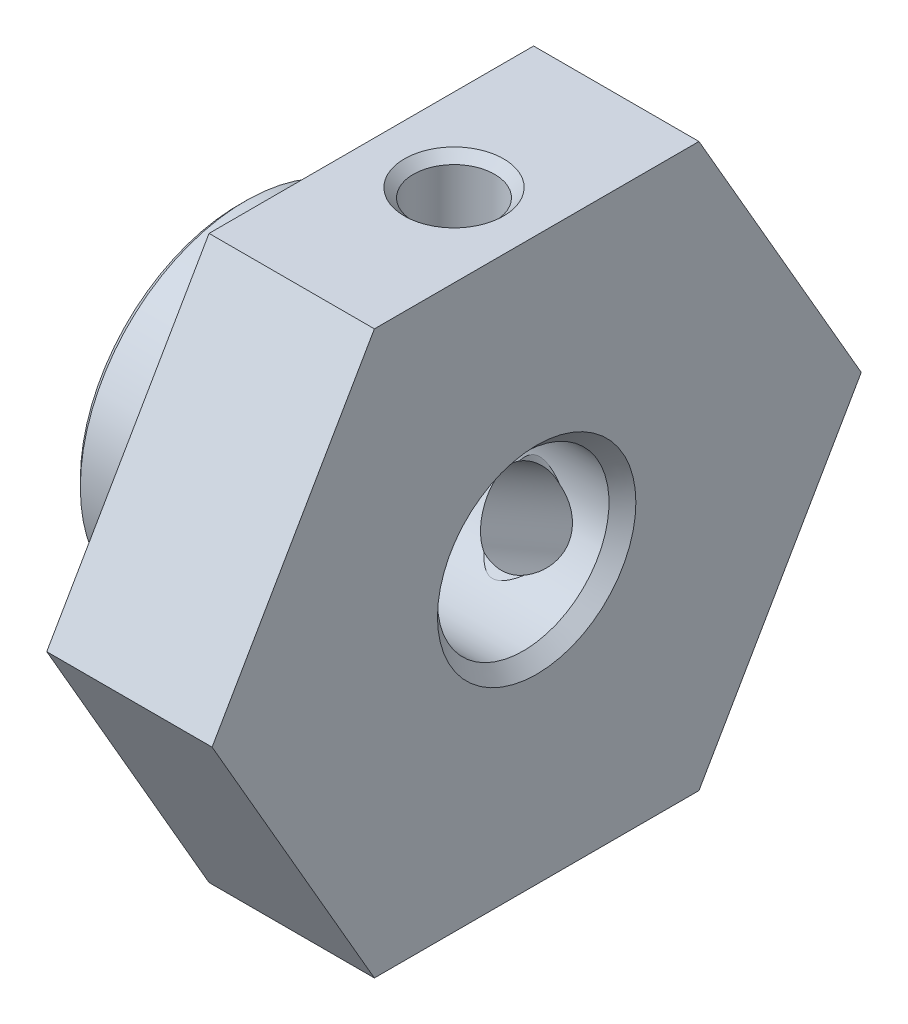
SolidWorks part; units mm, degrees
ref_plane "Front Plane" through (0, 0, 0) normal (0, 0, 1) x (1, 0, 0)
ref_plane "Top Plane" through (0, 0, 0) normal (0, 1, 0) x (1, 0, 0)
ref_plane "Right Plane" through (0, 0, 0) normal (1, 0, 0) x (0, 0, -1)
ref_plane "Plane1" through (0, 0, 0) normal (0, 0, 1) x (1, 0, 0)
sketch "Sketch1" plane through (0, 0, 0) normal (0, 0, 1) x (1, 0, 0)
  line L0 (0, 0) -> (0, 4.8)
  line L1 (0, 4.8) -> (0.2, 5)
  line L2 (0.2, 5) -> (4, 5)
  line L3 (4, 5) -> (4, 10.2)
  line L4 (4, 10.2) -> (9, 10.2)
  line L5 (9, 10.2) -> (9, 0)
  line L6 (9, 0) -> (0, 0)
  line L7 (9, 0) -> (0, 0) construction
revolve "Revolve1" add sketch "Sketch1" angle 360 about L7
ref_plane "Plane2" through (0, 0, 0) normal (0, 0, 1) x (1, 0, 0)
sketch "Sketch2" plane through (0, 0, 0) normal (0, 0, 1) x (1, 0, 0)
  line L0 (0, 0) -> (0, 3)
  line L1 (0, 3) -> (0.406, 2.594)
  line L2 (0.406, 2.594) -> (8.594, 2.594)
  line L3 (8.594, 2.594) -> (9, 3)
  line L4 (9, 3) -> (9, 0)
  line L5 (9, 0) -> (0, 0)
  line L6 (9, 0) -> (0, 0) construction
revolve "Cut-Revolve1" cut sketch "Sketch2" angle 360 about L6
ref_plane "Plane3" through (0, 0, 0) normal (1, 0, 0) x (0, 0, -1)
sketch "Sketch3" plane through (0, 0, 0) normal (1, 0, 0) x (0, 0, -1)
  line L0 (-17, -17) -> (17, -17)
  line L1 (17, -17) -> (17, 17)
  line L2 (17, 17) -> (-17, 17)
  line L3 (-17, 17) -> (-17, -17)
  line L4 (-9.815, 0) -> (-4.9075, -8.5)
  line L5 (-4.9075, -8.5) -> (4.9075, -8.5)
  line L6 (4.9075, -8.5) -> (9.815, 0)
  line L7 (9.815, 0) -> (4.9075, 8.5)
  line L8 (4.9075, 8.5) -> (-4.9075, 8.5)
  line L9 (-4.9075, 8.5) -> (-9.815, 0)
extrude "Cut-Extrude1" cut sketch "Sketch3" along normal blind 9
ref_plane "Plane4" through (6.5, 0, 0) normal (1, 0, 0) x (0, 0, -1)
sketch "Sketch4" plane through (6.5, 0, 0) normal (1, 0, 0) x (0, 0, -1)
  line L0 (0, 8.5) -> (1.5, 8.5)
  line L1 (1.5, 8.5) -> (1.2295, 8.2295)
  line L2 (1.2295, 8.2295) -> (1.2295, 2.3645)
  line L3 (1.2295, 2.3645) -> (1.5, 2.094)
  line L4 (1.5, 2.094) -> (0, 2.094)
  line L5 (0, 2.094) -> (0, 8.5)
  line L6 (0, 2.094) -> (0, 8.5) construction
revolve "Cut-Revolve2" cut sketch "Sketch4" angle 360 about L6
ref_plane "Plane5" through (6.5, 0, 0) normal (1, 0, 0) x (0, 0, -1)
sketch "Sketch5" plane through (6.5, 0, 0) normal (1, 0, 0) x (0, 0, -1)
  line L0 (7.3612, -4.25) -> (6.6112, -5.549)
  line L1 (6.6112, -5.549) -> (6.5122, -5.1795)
  line L2 (6.5122, -5.1795) -> (1.433, -2.247)
  line L3 (1.433, -2.247) -> (1.0635, -2.346)
  line L4 (1.0635, -2.346) -> (1.8135, -1.047)
  line L5 (1.8135, -1.047) -> (7.3612, -4.25)
  line L6 (1.8135, -1.047) -> (7.3612, -4.25) construction
revolve "Cut-Revolve3" cut sketch "Sketch5" angle 360 about L6
